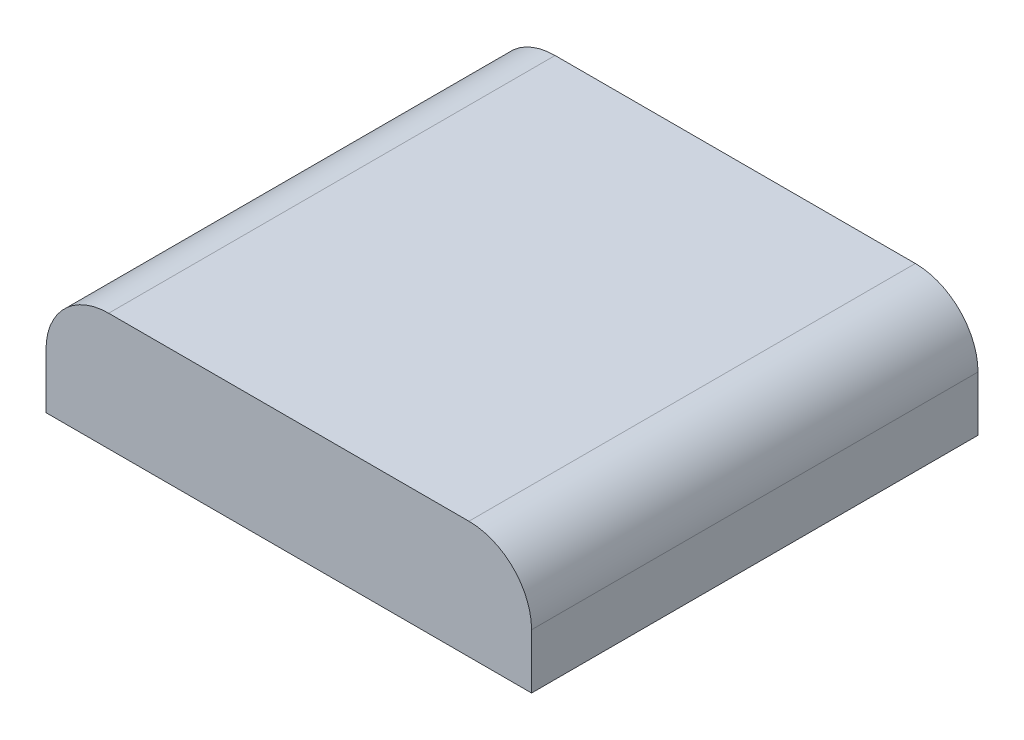
SolidWorks part; units mm, degrees
ref_plane "Front Plane" through (0, 0, 0) normal (0, 0, 1) x (1, 0, 0)
ref_plane "Top Plane" through (0, 0, 0) normal (0, 1, 0) x (1, 0, 0)
ref_plane "Right Plane" through (0, 0, 0) normal (1, 0, 0) x (0, 0, -1)
sketch "Sketch1" plane through (0, 0, 0) normal (0, 1, 0) x (1, 0, 0)
  line L1 (0, 0) -> (62, 0)
  line L2 (0, 0) -> (0, 57)
  line L3 (0, 57) -> (62, 57)
  line L4 (62, 0) -> (62, 57)
  dimension "D1" = 62
  dimension "D2" = 57
extrude "Boss-Extrude1" add sketch "Sketch1" along normal blind 15
fillet "Fillet1" radius 8 2 edges at (62, 15, -28.5) (0, 15, -28.5)
